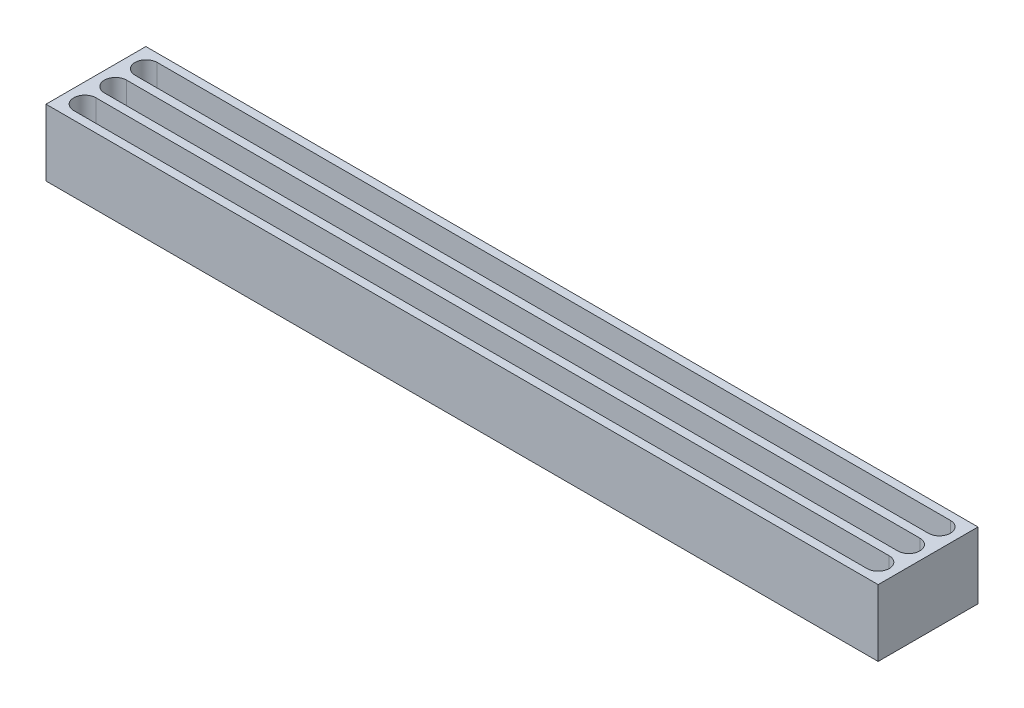
SolidWorks part; units mm, degrees
ref_plane "Front Plane" through (0, 0, 0) normal (0, 0, 1) x (1, 0, 0)
ref_plane "Top Plane" through (0, 0, 0) normal (0, 1, 0) x (1, 0, 0)
ref_plane "Right Plane" through (0, 0, 0) normal (1, 0, 0) x (0, 0, -1)
sketch "Sketch1" plane through (0, 0, 0) normal (0, 1, 0) x (1, 0, 0)
  line L0 (0, 38.1) -> (0, 31.75) construction
  line L1 (317.5, -38.1) -> (-317.5, -38.1)
  line L2 (317.5, -38.1) -> (317.5, 38.1)
  line L3 (317.5, 38.1) -> (-317.5, 38.1)
  line L4 (-317.5, -38.1) -> (-317.5, 38.1)
  line L5 (317.5, -38.1) -> (-317.5, 38.1) construction
  line L6 (317.5, 38.1) -> (-317.5, -38.1) construction
  line L7 (0, 31.75) -> (0, 14.8167) construction
  line L8 (302.6833, 0.0847) -> (-302.6833, 0.0847) construction
  line L9 (302.6833, -8.382) -> (-302.6833, -8.382)
  line L10 (0, -38.1) -> (0, -23.2833) construction
  line L11 (302.6833, -23.2833) -> (-302.6833, -23.2833) construction
  line L12 (302.6833, -31.75) -> (-302.6833, -31.75)
  line L13 (302.6833, -14.8167) -> (-302.6833, -14.8167)
  line L14 (302.6833, 8.5513) -> (-302.6833, 8.5513)
  line L15 (302.6833, 23.4527) -> (-302.6833, 23.4527) construction
  line L16 (302.6833, 14.986) -> (-302.6833, 14.986)
  line L17 (302.6833, 31.9193) -> (-302.6833, 31.9193)
  arc A0 (302.6833, -31.75) -> (302.6833, -14.8167) centre (302.6833, -23.2833) ccw
  arc A1 (-302.6833, -14.8167) -> (-302.6833, -31.75) centre (-302.6833, -23.2833) ccw
  arc A2 (302.6833, -8.382) -> (302.6833, 8.5513) centre (302.6833, 0.0847) ccw
  arc A3 (-302.6833, 8.5513) -> (-302.6833, -8.382) centre (-302.6833, 0.0847) ccw
  arc A4 (302.6833, 14.986) -> (302.6833, 31.9193) centre (302.6833, 23.4527) ccw
  arc A5 (-302.6833, 31.9193) -> (-302.6833, 14.986) centre (-302.6833, 23.4527) ccw
  point P0 (0, 0)
  point P15 (0, -23.2833)
  point P21 (0, 0.0847)
  point P28 (0, 23.4527)
  dimension "D8" = 8.4667
  dimension "D1" = 635
  dimension "D2" = 76.2
  dimension "D3" = 6.35
  dimension "D4" = 16.9333
  dimension "D5" = 3
  dimension "D7" = 14.8167
  dimension "D9" = 14.8167
extrude "Boss-Extrude1" add sketch "Sketch1" against normal blind 50.8
